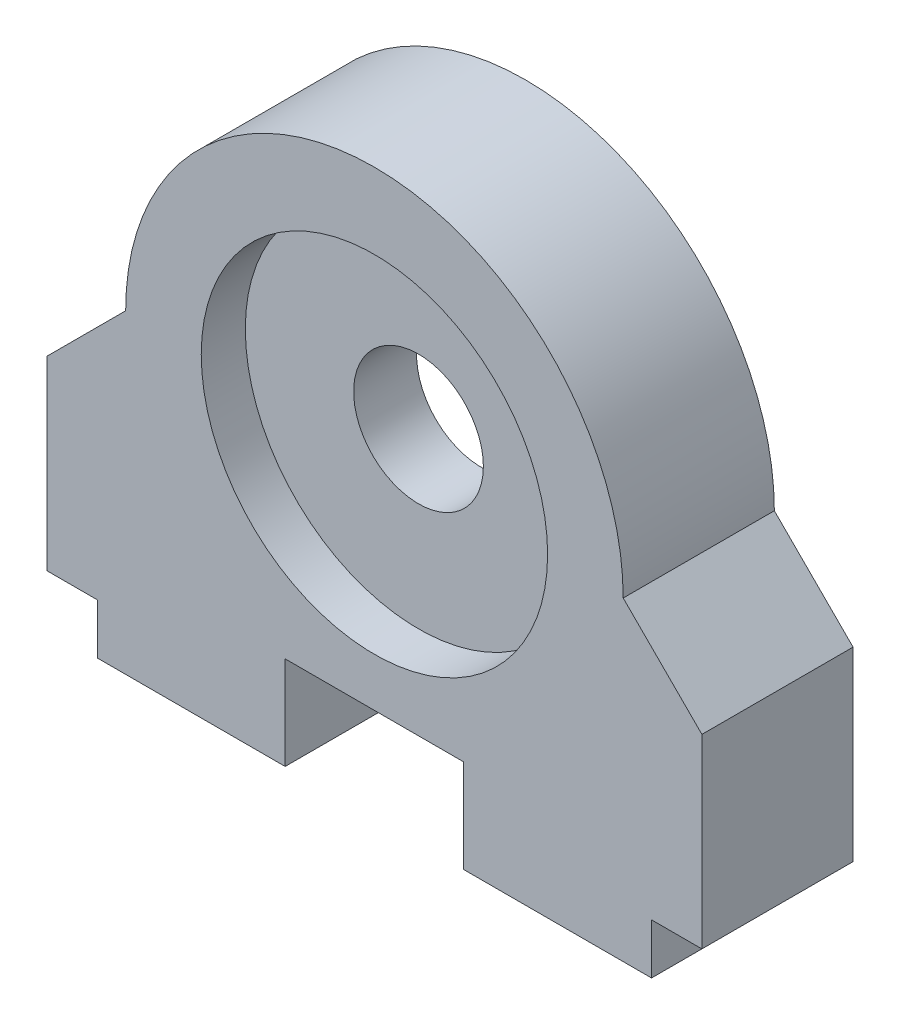
SolidWorks part; units mm, degrees
ref_plane "Front Plane" through (0, 0, 0) normal (0, 0, 1) x (1, 0, 0)
ref_plane "Top Plane" through (0, 0, 0) normal (0, 1, 0) x (1, 0, 0)
ref_plane "Right Plane" through (0, 0, 0) normal (1, 0, 0) x (0, 0, -1)
sketch "Sketch1" plane through (0, 0, 0) normal (0, 0, 1) x (1, 0, 0)
  line L0 (0, -26.1041) -> (0, 52.7781) construction
  line L1 (4.5, 4.699) -> (-4.5, 4.699)
  line L2 (-4.5, 4.699) -> (-4.5, 0)
  line L3 (-4.5, 0) -> (-13.97, 0)
  line L4 (16.51, 2.54) -> (16.51, 11.9063)
  line L5 (16.51, 11.9063) -> (12.5412, 15.875)
  line L6 (4.5, 4.699) -> (4.5, 0)
  line L7 (-16.51, 2.54) -> (-16.51, 11.9063)
  line L8 (4.5, 0) -> (13.97, 0)
  line L9 (-16.51, 11.9063) -> (-12.5412, 15.875)
  line L10 (16.51, 2.54) -> (13.97, 2.54)
  line L11 (13.97, 0) -> (13.97, 2.54)
  line L13 (-16.51, 2.54) -> (-13.97, 2.54)
  line L14 (-13.97, 0) -> (-13.97, 2.54)
  circle A0 centre (0, 15.875) radius 8.7312
  arc A1 (-12.5412, 15.875) -> (12.5412, 15.875) centre (0, 15.875) cw
  point P11 (0, 4.699)
  point P12 (0, 28.448)
  point P15 (0, 7.1438)
  dimension "D6" = 17.4625
  dimension "D3" = 3.81
  dimension "D1" = 9
  dimension "D2" = 4.699
  dimension "D4" = 45
  dimension "D5" = 15.875
  dimension "D7" = 33.02
  dimension "D8" = 2.54
  dimension "D9" = 2.54
extrude "Boss-Extrude1" add sketch "Sketch1" along normal blind 7.62
ref_plane "Plane1" through (0, 0, 3.81) normal (0, 0, 1) x (1, 0, 0)
sketch "Sketch3" plane through (0, 0, 3.81) normal (0, 0, 1) x (1, 0, 0)
  circle A0 centre (0, 15.875) radius 3.2703
  circle A1 centre (0, 15.875) radius 8.7376
  dimension "D1" = 6.5405
  dimension "D2" = 17.4752
extrude "Boss-Extrude2" add sketch "Sketch3" along normal blind 1.5875 and the other way blind 1.5875
sketch "Sketch4" plane through (0, 0, 0) normal (0, -1, 0) x (-1, 0, 0)
  line L0 (-4.5, 0) -> (-13.97, 0) construction
  line L3 (0, 9.7586) -> (0, -18.8259) construction
  circle A0 centre (-10.16, -3.81) radius 1.9837
  circle A1 centre (10.16, -3.81) radius 1.9837
  dimension "D1" = 3.9675
  dimension "D2" = 10.16
  dimension "D3" = 3.81
extrude "Cut-Extrude1" cut sketch "Sketch4" against normal blind 10.16
equation "\"0.095inin\"=0.085"
